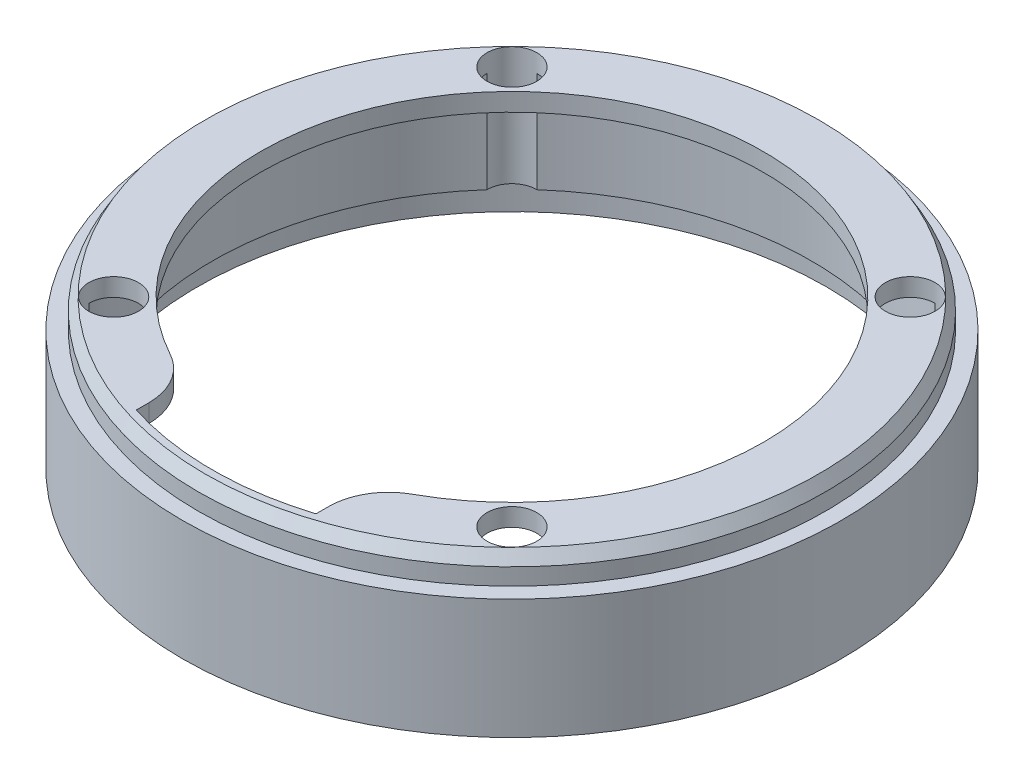
SolidWorks part; units mm, degrees
ref_plane "Спереди" through (0, 0, 0) normal (0, 0, 1) x (1, 0, 0)
ref_plane "Сверху" through (0, 0, 0) normal (0, 1, 0) x (1, 0, 0)
ref_plane "Справа" through (0, 0, 0) normal (1, 0, 0) x (0, 0, -1)
sketch "Sketch1" plane through (0, 0, 0) normal (0, 1, 0) x (1, 0, 0)
  circle A0 centre (0, 0) radius 55
  dimension "D1" = 110
extrude "Boss-Extrude1" add sketch "Sketch1" along normal blind 24.8
shell "Shell1" thickness 5
sketch "Sketch2" plane through (0, 19.8, 0) normal (0, -1, 0) x (1, 0, 0)
  circle A0 centre (0, 0) radius 35
  dimension "D1" = 70
extrude "Cut-Extrude1" cut sketch "Sketch2" against normal through all
sketch "Sketch3" plane through (0, 24.8, 0) normal (0, 1, 0) x (1, 0, 0)
  circle A0 centre (0, 0) radius 42
  dimension "D1" = 84
extrude "Cut-Extrude2" cut sketch "Sketch3" against normal through all
sketch "Sketch4" plane through (0, 24.8, 0) normal (0, 1, 0) x (1, 0, 0)
  line L1 (-33.234, 33.234) -> (33.234, 33.234) construction
  line L2 (-33.234, 33.234) -> (-33.234, -33.234) construction
  line L3 (-33.234, -33.234) -> (33.234, -33.234) construction
  line L4 (33.234, 33.234) -> (33.234, -33.234) construction
  line L5 (-33.234, 33.234) -> (33.234, -33.234) construction
  line L6 (-33.234, -33.234) -> (33.234, 33.234) construction
  circle A0 centre (0, 0) radius 55 construction
  circle A2 centre (-33.234, -33.234) radius 4.15
  circle A3 centre (-33.234, 33.234) radius 4.15
  circle A4 centre (33.234, 33.234) radius 4.15
  circle A5 centre (33.234, -33.234) radius 4.15
  circle A6 centre (0, 0) radius 47 construction
  dimension "D2" = 8.3
  dimension "D3" = 8
extrude "Cut-Extrude3" cut sketch "Sketch4" against normal through all
sketch "Sketch6" plane through (0, 19.8, 0) normal (0, -1, 0) x (1, 0, 0)
  circle A0 centre (0, 0) radius 50
extrude "Cut-Extrude4" cut sketch "Sketch6" against normal blind 2
sketch "Sketch7" plane through (0, 21.8, 0) normal (0, -1, 0) x (1, 0, 0)
  line L0 (33.234, 33.234) -> (-33.234, 33.234) construction
  line L1 (0, 33.234) -> (0, 50) construction
  line L2 (15, 33.234) -> (15, 47.697)
  line L3 (-15, 33.234) -> (-15, 47.697)
  line L4 (15, 33.234) -> (-15, 33.234)
  arc A0 (33.2031, 37.3839) -> (-33.2031, 37.3839) centre (0, 0) ccw construction
  arc A1 (15, 47.697) -> (-15, 47.697) centre (0, 0) ccw
  point P14 (0, 33.234)
  dimension "D1" = 30
extrude "Cut-Extrude5" cut sketch "Sketch7" against normal through all
fillet "Fillet1" radius 10 2 edges at (-15, 23.3, 39.2301) (15, 23.3, 39.2301)
sketch "Sketch8" plane through (0, 24.8, 0) normal (0, 1, 0) x (1, 0, 0)
  circle A0 centre (0, 0) radius 52.35
  dimension "D1" = 104.7
extrude "Cut-Extrude6" cut sketch "Sketch8" against normal blind 4.8 flip side to cut
chamfer "Chamfer1" distance 2 angle 30 1 edges at (0, 24.8, 52.35)
sketch "Sketch9" plane through (0, 0, 0) normal (0, -1, 0) x (1, 0, 0)
  circle A0 centre (0, 0) radius 52.5
  dimension "D1" = 105
extrude "Cut-Extrude7" cut sketch "Sketch9" against normal blind 5
